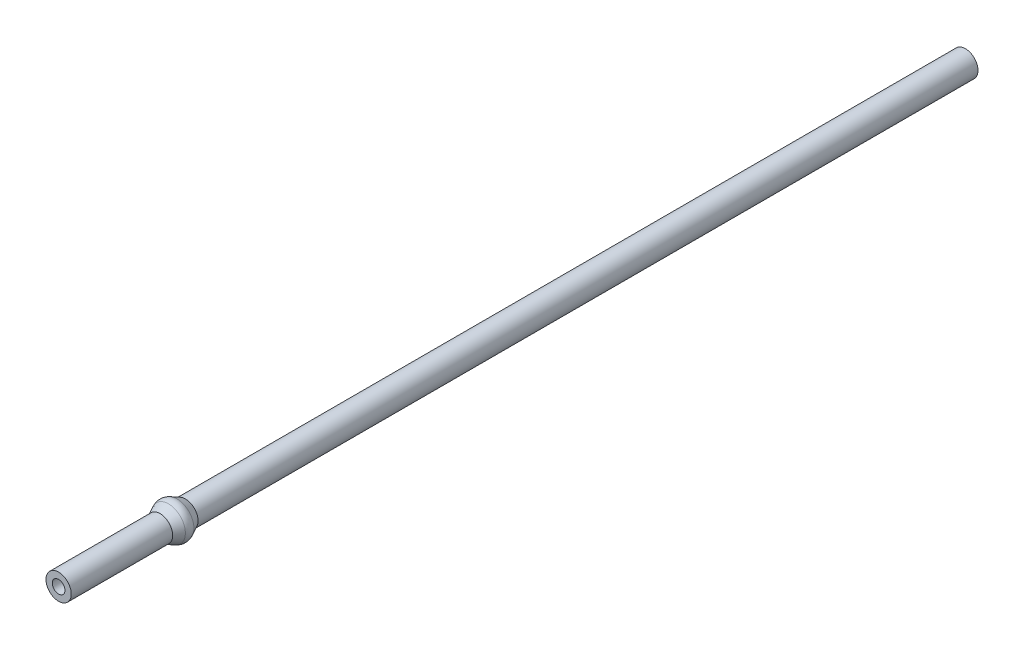
SolidWorks part; units mm, degrees
ref_plane "Front Plane" through (0, 0, 0) normal (0, 0, 1) x (1, 0, 0)
ref_plane "Top Plane" through (0, 0, 0) normal (0, 1, 0) x (1, 0, 0)
ref_plane "Right Plane" through (0, 0, 0) normal (1, 0, 0) x (0, 0, -1)
sketch "Sketch1" plane through (0, 0, 0) normal (0, 0, 1) x (1, 0, 0)
  circle A0 centre (0, 0) radius 1.5824
  dimension "D1" = 3.1648
extrude "Boss-Extrude1" add sketch "Sketch1" against normal blind 113.5062
sketch "Sketch2" plane through (0, 0, 0) normal (0, 0, 1) x (1, 0, 0)
  circle A0 centre (0, 0) radius 0.7937
  dimension "D1" = 1.5875
extrude "Cut-Extrude1" cut sketch "Sketch2" against normal blind 3.175
sketch "Sketch3" plane through (0, 0, 0) normal (0, 0, 1) x (1, 0, 0)
  circle A0 centre (0, 0) radius 0.3969
  dimension "D1" = 0.7937
extrude "Cut-Extrude2" cut sketch "Sketch3" against normal blind 14.2875
sketch "Sketch4" plane through (0, 0, 0) normal (0, 0, 1) x (1, 0, 0)
  circle A0 centre (0, 0) radius 0.7937
  dimension "D1" = 1.5875
extrude "Cut-Extrude4" cut sketch "Sketch4" against normal through all from offset 14.2875 offset against normal yes
sketch "Sketch5" plane through (0, 0, 0) normal (1, 0, 0) x (0, 0, -1)
  line L0 (12.7, 1.5824) -> (13.752, 2.1118)
  line L1 (113.5062, 1.5824) -> (0, 1.5824) construction
  line L2 (14.823, 2.1118) -> (15.875, 1.5824)
  line L3 (15.875, 1.5824) -> (12.7, 1.5824)
  line L4 (0, 1.5824) -> (0, -1.5824) construction
  line L5 (0, 0) -> (20.4295, 0) construction
  arc A0 (13.752, 2.1118) -> (14.823, 2.1118) centre (14.2875, 1.0477) cw
  point P10 (14.2875, 2.3813)
  dimension "D5" = 1.1913
  dimension "D1" = 12.7
  dimension "D2" = 15.875
  dimension "D3" = 14.2875
  dimension "D4" = 2.3813
revolve "Revolve1" add sketch "Sketch5" angle 360 about L5
